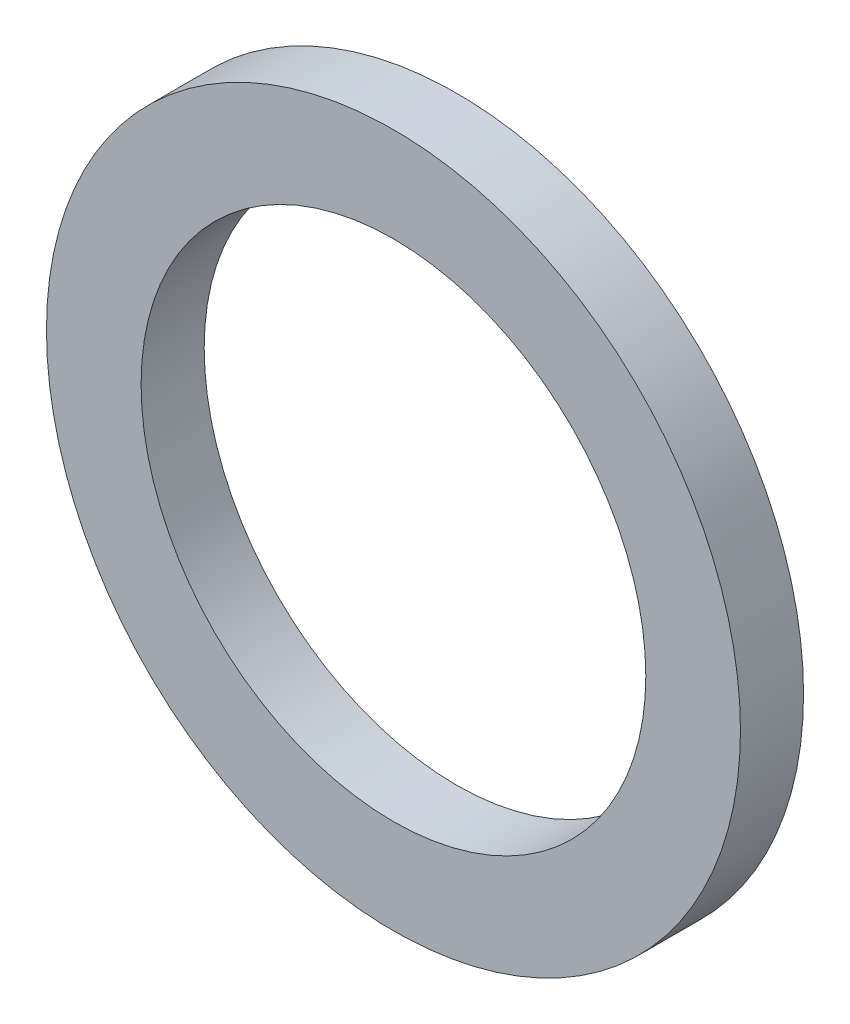
SolidWorks part; units mm, degrees
ref_plane "Front Plane" through (0, 0, 0) normal (0, 0, 1) x (1, 0, 0)
ref_plane "Top Plane" through (0, 0, 0) normal (0, 1, 0) x (1, 0, 0)
ref_plane "Right Plane" through (0, 0, 0) normal (1, 0, 0) x (0, 0, -1)
sketch "Sketch1" plane through (0, 0, 0) normal (0, 0, 1) x (1, 0, 0)
  circle A0 centre (0, 0) radius 4
  dimension "D1" = 8
extrude "Extrude-Thin1" add sketch "Sketch1" along normal blind 1 thin
